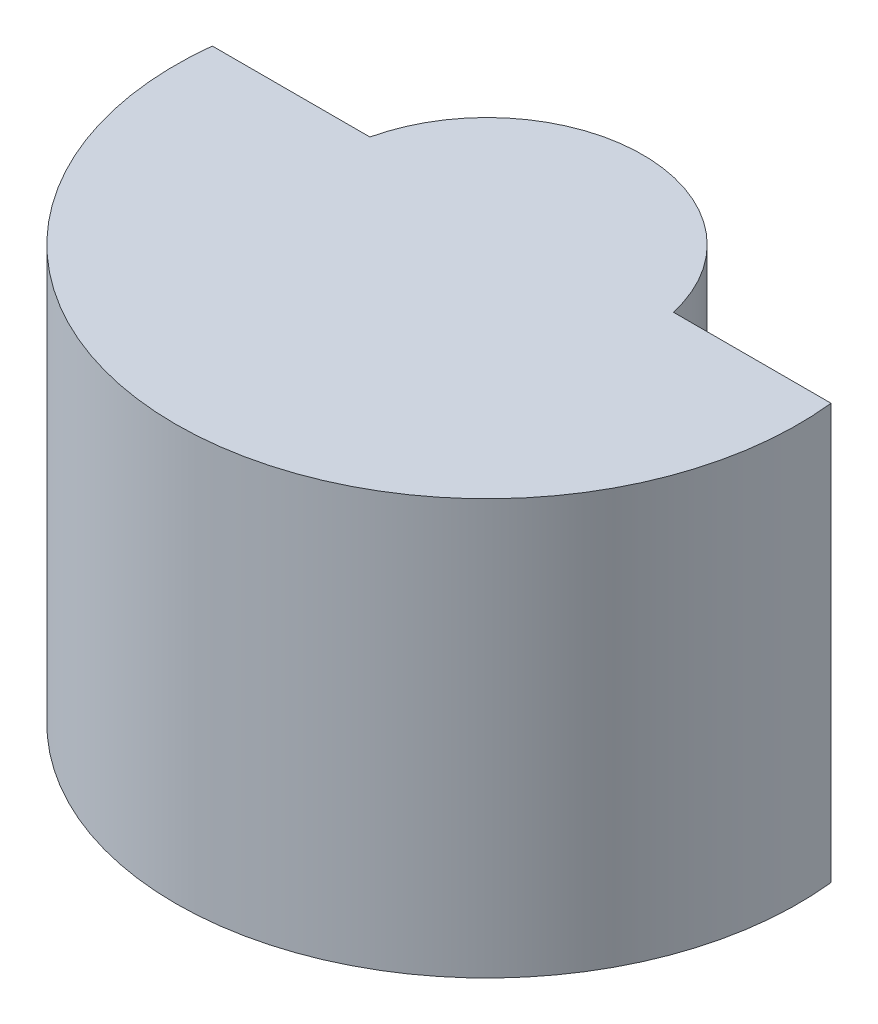
SolidWorks part; units mm, degrees
ref_plane "Ebene vorne" through (0, 0, 0) normal (0, 0, 1) x (1, 0, 0)
ref_plane "Ebene oben" through (0, 0, 0) normal (0, 1, 0) x (1, 0, 0)
ref_plane "Ebene rechts" through (0, 0, 0) normal (1, 0, 0) x (0, 0, -1)
sketch "Skizze2" plane through (0, 75.95, 0) normal (0, 1, 0) x (1, 0, 0)
  line L0 (-4.4721, 0) -> (-2.1937, 0)
  line L1 (2.1937, 0) -> (4.4721, 0)
  line L2 (-2.1937, 0) -> (2.1937, 0) construction
  line L3 (0, -0.5) -> (0, -5) construction
  line L4 (-2.4495, 0) -> (-72.5, 0) construction
  arc A1 (-2.1937, 0) -> (2.1937, 0) centre (0, -0.5) cw
  arc A2 (-4.4721, 0) -> (4.4721, 0) centre (0, -0.5) ccw
  arc A3 (2.4495, 0) -> (-2.4495, 0) centre (0, -0.5) ccw construction
  circle A4 centre (0, -0.5) radius 4.5 construction
  dimension "D1" = 0.25
extrude "Aufsatz-Linear austragen1" add sketch "Skizze2" along normal blind 6 from offset 0.5
ref_plane "Ebene2" through (0, 79.45, 0) normal (0, -1, 0) x (-1, 0, 0)
sketch "Skizze6" plane through (0, 79.45, 0) normal (0, -1, 0) x (-1, 0, 0)
  line L0 (0, 1.75) -> (0, -3.0261) construction
  line L2 (-1.7, 0.9739) -> (-1.7, -3.0261)
  line L3 (-1.7, -3.0261) -> (0, -3.0261)
  line L5 (0, -3.0261) -> (0, 1.75)
  line L6 (-1.7, 0.9739) -> (-1.7, 1.9)
  line L8 (-1.7, 1.9) -> (0, 1.9)
  line L9 (0, 1.9) -> (0, 1.75)
  arc A2 (2.1937, 0) -> (-2.1937, 0) centre (0, -0.5) ccw construction
  dimension "D1" = 0.15
  dimension "D2" = 4
  dimension "D3" = 1.7
revolve "Schnitt-Rotation4" cut sketch "Skizze6" angle 360 about L0
equation "\"M2EinschmelzGewindeDurchmesser\"=3.4"
equation "\"M2EinschmelzGewindeTiefe\"= 4.0"
equation "\"M3EinschmelzGewindeDurchmesser\"= 4.2"
equation "\"M3EinschmelzGewindeTief\"= 5.7"
equation "\"M2SchraubeLoch\"=2.3"
equation "\"offSetVonGummiReifen\"= 3.0"
equation "\"D2@Skizze6\"=\"M2EinschmelzGewindeTiefe\""
equation "\"D3@Skizze6\"=\"M2EinschmelzGewindeDurchmesser\" / 2"
